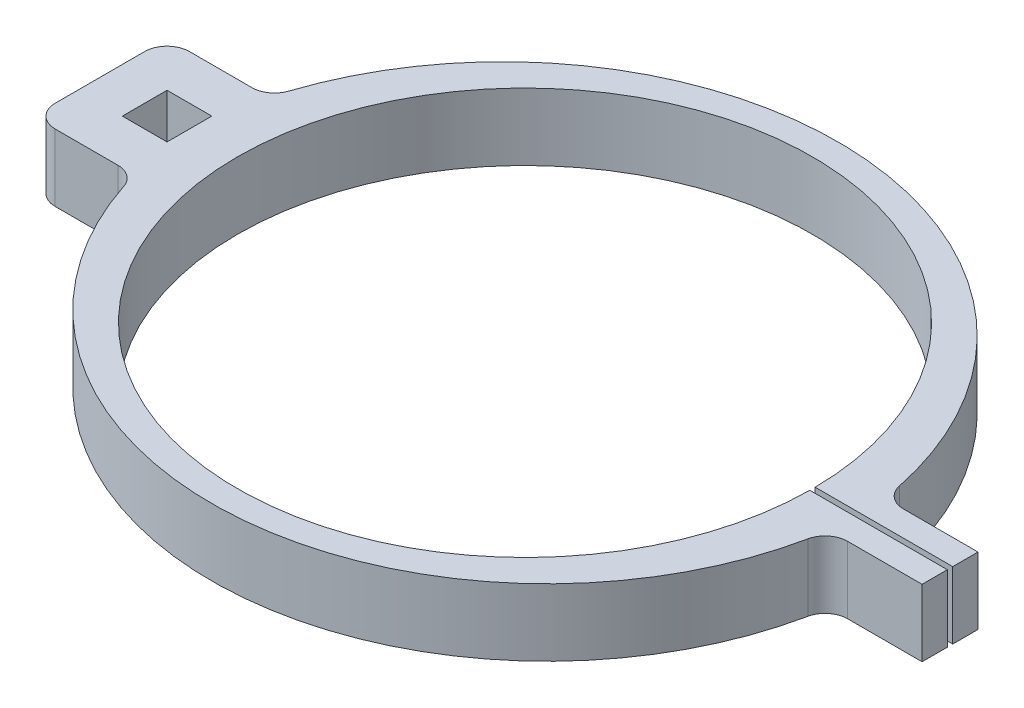
SolidWorks part; units mm, degrees
ref_plane "Front Plane" through (0, 0, 0) normal (0, 0, 1) x (1, 0, 0)
ref_plane "Top Plane" through (0, 0, 0) normal (0, 1, 0) x (1, 0, 0)
ref_plane "Right Plane" through (0, 0, 0) normal (1, 0, 0) x (0, 0, -1)
sketch "Sketch1" plane through (0, 0, 0) normal (0, 1, 0) x (1, 0, 0)
  line L0 (0, 0) -> (60.2074, 0) construction
  line L1 (40.8033, -0.381) -> (60.325, -0.381)
  line L2 (-53.975, 3.175) -> (-47.625, 3.175)
  line L3 (-53.975, 3.175) -> (-53.975, -3.175)
  line L4 (-53.975, -3.175) -> (-47.625, -3.175)
  line L5 (-47.625, 3.175) -> (-47.625, -3.175)
  line L6 (-53.975, 3.175) -> (-47.625, -3.175) construction
  line L7 (-53.975, -3.175) -> (-47.625, 3.175) construction
  line L8 (40.8033, 0.381) -> (60.325, 0.381)
  line L9 (47.0862, -3.9688) -> (60.325, -3.9688)
  line L10 (47.0862, 3.9688) -> (60.325, 3.9688)
  line L11 (-60.325, 9.525) -> (-45.9004, 9.525)
  line L12 (-60.325, -9.525) -> (-45.9004, -9.525)
  line L13 (-60.325, 9.525) -> (-60.325, -9.525)
  line L14 (-60.325, 3.175) -> (-60.325, -3.175) construction
  line L15 (-53.975, 9.525) -> (-47.625, 9.525) construction
  line L16 (-53.975, -9.525) -> (-47.625, -9.525) construction
  line L17 (60.325, 3.9688) -> (60.325, 0.381)
  line L18 (0, 3.9688) -> (60.2074, 3.9688) construction
  line L19 (0, -3.9688) -> (60.2074, -3.9688) construction
  line L20 (0, -0.381) -> (60.2074, -0.381) construction
  line L21 (0, 0.381) -> (60.2074, 0.381) construction
  line L22 (60.325, -0.381) -> (60.325, -3.9688)
  arc A0 (40.8033, 0.381) -> (40.8033, -0.381) centre (0, 0) ccw
  arc A2 (-45.9004, -9.525) -> (47.0862, -3.9688) centre (0, 3.175) ccw
  arc A3 (47.0862, 3.9688) -> (-45.9004, 9.525) centre (0, -3.175) ccw
  point P7 (-50.8, 0)
  dimension "D3" = 81.6102
  dimension "D4" = 60.325
  dimension "D12" = 95.25
  dimension "D1" = 3.175
  dimension "D2" = 3.175
  dimension "D13" = 13.2388
  dimension "D14" = 6.35
  dimension "D15" = 50.8
  dimension "D5" = 0.381
  dimension "D6" = 0.381
  dimension "D7" = 3.9688
  dimension "D8" = 3.9688
  dimension "D9" = 6.35
  dimension "D10" = 6.35
  dimension "D11" = 6.35
extrude "Boss-Extrude1" add sketch "Sketch1" along normal mid plane 9.525
fillet "Fillet1" radius 3.175 6 edges at (47.0862, 0, -3.9688) (47.0862, 0, 3.9688) (-45.9004, 0, -9.525) (-60.325, 0, -9.525) (-60.325, 0, 9.525) (-45.9004, 0, 9.525)
equation "\"Buoyancy\"=\"SW-Volume\"*(\"SW-Density\"-.037062)"
